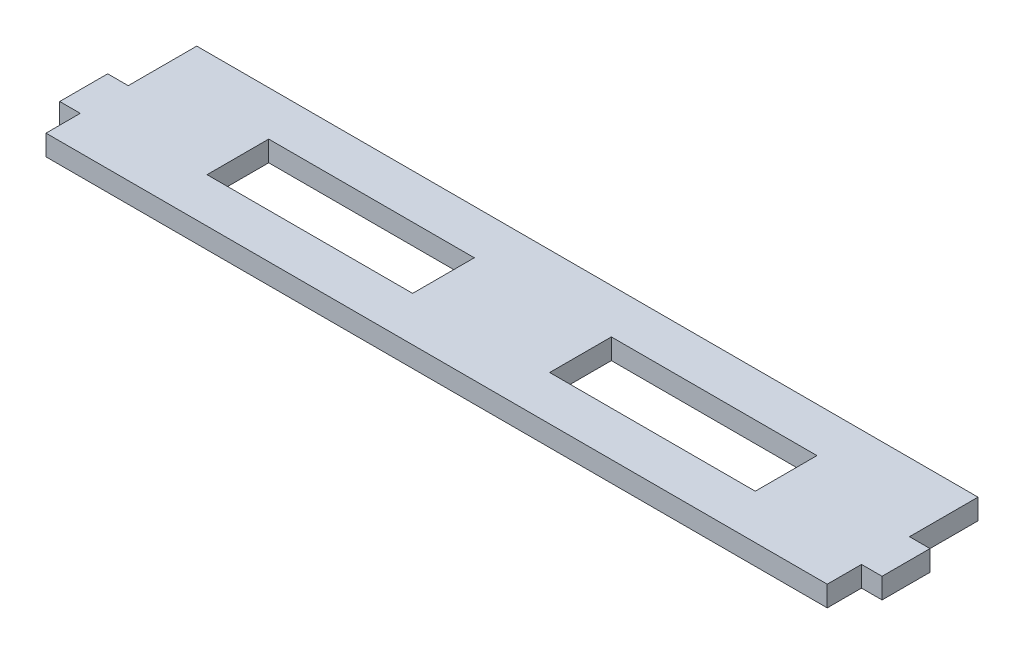
SolidWorks part; units mm, degrees
ref_plane "Alzado" through (0, 0, 0) normal (0, 0, 1) x (1, 0, 0)
ref_plane "Planta" through (0, 0, 0) normal (0, 1, 0) x (1, 0, 0)
ref_plane "Vista lateral" through (0, 0, 0) normal (1, 0, 0) x (0, 0, -1)
sketch "Croquis1" plane through (0, 0, 0) normal (0, 1, 0) x (1, 0, 0)
  line L0 (-57, 1) -> (-60, 1)
  line L1 (57, 11) -> (-57, 11)
  line L2 (57, 11) -> (57, 1)
  line L3 (57, -11) -> (-57, -11)
  line L4 (-57, 11) -> (-57, 1)
  line L5 (57, 11) -> (-57, -11) construction
  line L6 (57, -11) -> (-57, 11) construction
  line L11 (-60, 1) -> (-60, -6)
  line L12 (-60, -6) -> (-57, -6)
  line L13 (-57, -6) -> (-57, -11)
  line L14 (0, 0) -> (0, -35.1728) construction
  line L15 (57, 1) -> (60, 1)
  line L16 (60, 1) -> (60, -6)
  line L17 (60, -6) -> (57, -6)
  line L18 (57, -6) -> (57, -11)
  point P0 (0, 0)
  dimension "D1" = 22
  dimension "D2" = 120
  dimension "D3" = 3
  dimension "D4" = 7
  dimension "D5" = 10
extrude "Saliente-Extruir1" add sketch "Croquis1" along normal blind 3
sketch "Croquis2" plane through (0, 3, 0) normal (0, 1, 0) x (1, 0, 0)
  line L0 (0, 0) -> (83.4428, 0) construction
  line L1 (-10, -4.5) -> (-40, -4.5)
  line L2 (-10, -4.5) -> (-10, 4.5)
  line L3 (-10, 4.5) -> (-40, 4.5)
  line L4 (-40, -4.5) -> (-40, 4.5)
  line L5 (-10, -4.5) -> (-40, 4.5) construction
  line L6 (-10, 4.5) -> (-40, -4.5) construction
  line L7 (40, -4.5) -> (10, -4.5)
  line L8 (40, -4.5) -> (40, 4.5)
  line L9 (40, 4.5) -> (10, 4.5)
  line L10 (10, -4.5) -> (10, 4.5)
  line L11 (40, -4.5) -> (10, 4.5) construction
  line L12 (40, 4.5) -> (10, -4.5) construction
  line L13 (0, 0) -> (0, -35.0791) construction
  point P0 (-25, 0)
  point P5 (25, 0)
  dimension "D1" = 30
  dimension "D2" = 9
  dimension "D3" = 30
  dimension "D4" = 9
  dimension "D5" = 20
extrude "Cortar-Extruir1" cut sketch "Croquis2" against normal through all
